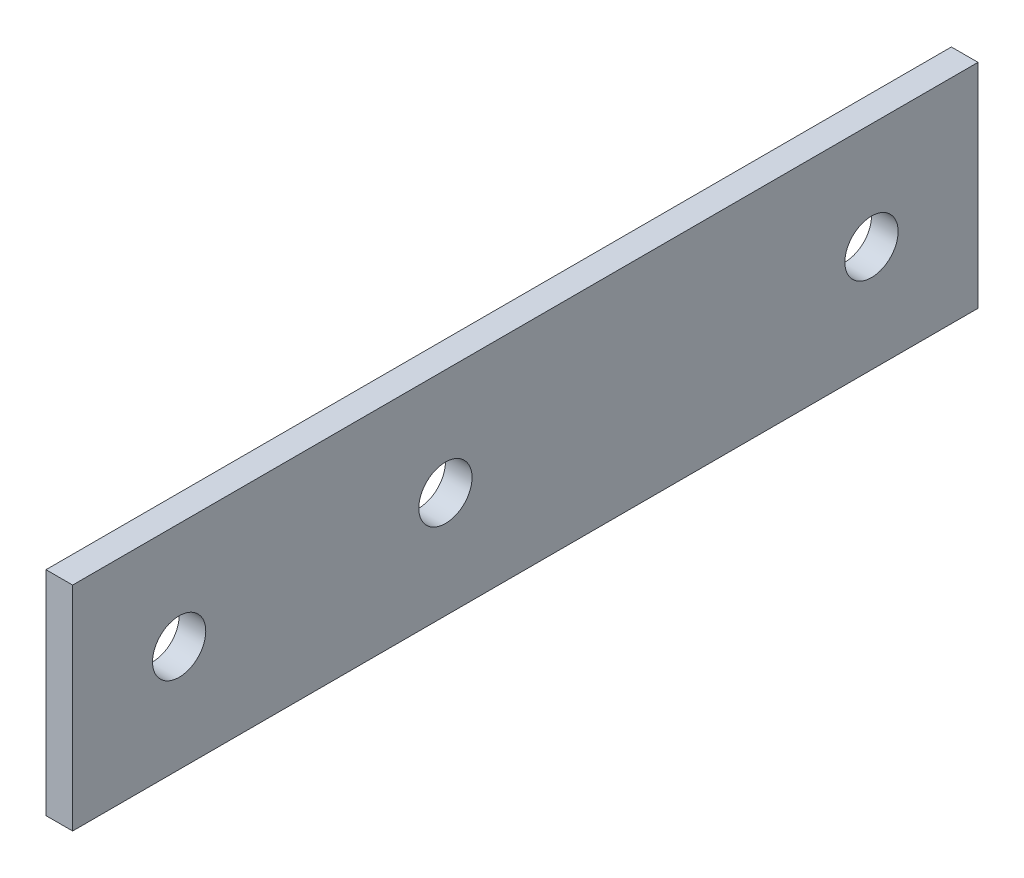
SolidWorks part; units mm, degrees
material "6061-T6 (SS)"
ref_plane "Front Plane" through (0, 0, 0) normal (0, 0, 1) x (1, 0, 0)
ref_plane "Top Plane" through (0, 0, 0) normal (0, 1, 0) x (1, 0, 0)
ref_plane "Right Plane" through (0, 0, 0) normal (1, 0, 0) x (0, 0, -1)
sketch "Sketch1" plane through (0, 0, 0) normal (1, 0, 0) x (0, 0, -1)
  line L1 (53.975, -12.7) -> (-53.975, -12.7)
  line L2 (53.975, -12.7) -> (53.975, 12.7)
  line L3 (53.975, 12.7) -> (-53.975, 12.7)
  line L4 (-53.975, -12.7) -> (-53.975, 12.7)
  line L5 (53.975, -12.7) -> (-53.975, 12.7) construction
  line L6 (53.975, 12.7) -> (-53.975, -12.7) construction
  point P0 (0, 0)
  dimension "D1" = 25.4
  dimension "D2" = 107.95
extrude "Boss-Extrude1" add sketch "Sketch1" along normal blind 3.175
sketch "Sketch2" plane through (3.175, 0, 0) normal (1, 0, 0) x (0, 0, -1)
  circle A0 centre (41.275, 0) radius 3.175 construction
  circle A1 centre (-9.525, 0) radius 3.175 construction
  circle A2 centre (-41.275, 0) radius 3.175 construction
  circle A3 centre (41.275, 0) radius 3.175
  circle A4 centre (-9.525, 0) radius 3.175
  circle A5 centre (-41.275, 0) radius 3.175
extrude "Cut-Extrude1" cut sketch "Sketch2" against normal through all
